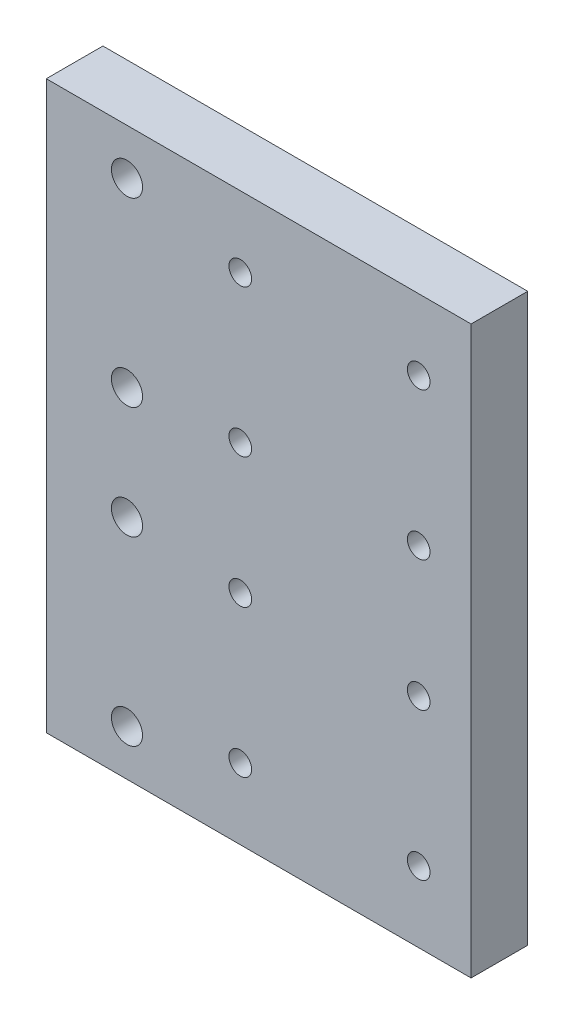
SolidWorks part; units mm, degrees
ref_plane "Ön Düzlem" through (0, 0, 0) normal (0, 0, 1) x (1, 0, 0)
ref_plane "Üst Düzlem" through (0, 0, 0) normal (0, 1, 0) x (1, 0, 0)
ref_plane "Sağ Düzlem" through (0, 0, 0) normal (1, 0, 0) x (0, 0, -1)
sketch "Sketch1" plane through (0, 0, 0) normal (0, 0, 1) x (1, 0, 0)
  line L0 (0, -50) -> (0, 50)
  line L1 (0, 50) -> (-75, 50)
  line L3 (-75, -50) -> (0, -50)
  line L4 (-25, 24.5) -> (-25, -24.5) construction
  line L11 (-40.75, 11.5) -> (-9.25, 11.5) construction
  line L12 (-40.75, 11.5) -> (-40.75, 37.5) construction
  line L13 (-40.75, 37.5) -> (-9.25, 37.5) construction
  line L14 (-9.25, 11.5) -> (-9.25, 37.5) construction
  line L15 (-40.75, 11.5) -> (-9.25, 37.5) construction
  line L16 (-40.75, 37.5) -> (-9.25, 11.5) construction
  line L17 (-40.75, -37.5) -> (-9.25, -37.5) construction
  line L18 (-40.75, -37.5) -> (-40.75, -11.5) construction
  line L19 (-40.75, -11.5) -> (-9.25, -11.5) construction
  line L20 (-9.25, -37.5) -> (-9.25, -11.5) construction
  line L21 (-40.75, -37.5) -> (-9.25, -11.5) construction
  line L22 (-40.75, -11.5) -> (-9.25, -37.5) construction
  line L25 (-60.75, 41.9046) -> (-60.75, 9.9046) construction
  line L26 (-60.75, -9.9046) -> (-60.75, -41.9046) construction
  line L27 (-60.75, 25.9046) -> (-60.75, -25.9046) construction
  line L28 (-75, 50) -> (-75, -50)
  circle A5 centre (-40.75, 37.5) radius 2
  circle A6 centre (-9.25, 37.5) radius 2
  circle A7 centre (-40.75, 11.5) radius 2
  circle A8 centre (-9.25, 11.5) radius 2
  circle A9 centre (-40.75, -11.5) radius 2
  circle A10 centre (-9.25, -11.5) radius 2
  circle A11 centre (-9.25, -37.5) radius 2
  circle A12 centre (-40.75, -37.5) radius 2
  circle A13 centre (-60.75, 41.9046) radius 2.75
  circle A14 centre (-60.75, 9.9046) radius 2.75
  circle A15 centre (-60.75, -9.9046) radius 2.75
  circle A16 centre (-60.75, -41.9046) radius 2.75
  point P3 (0, 0)
  point P4 (0, 0)
  point P6 (0, 0)
  point P16 (-25, -24.5)
  point P19 (-25, 24.5)
  point P29 (-25, 0)
  point P51 (-60.75, 0)
  dimension "D11" = 4
  dimension "D13" = 5.5
  dimension "D16" = 20
  dimension "D1" = 100
  dimension "D2" = 75
  dimension "D7" = 31.5
  dimension "D8" = 26
  dimension "D9" = 23
  dimension "D10" = 25
  dimension "D12" = 32
extrude "Boss-Extrude1" add sketch "Sketch1" along normal blind 10
